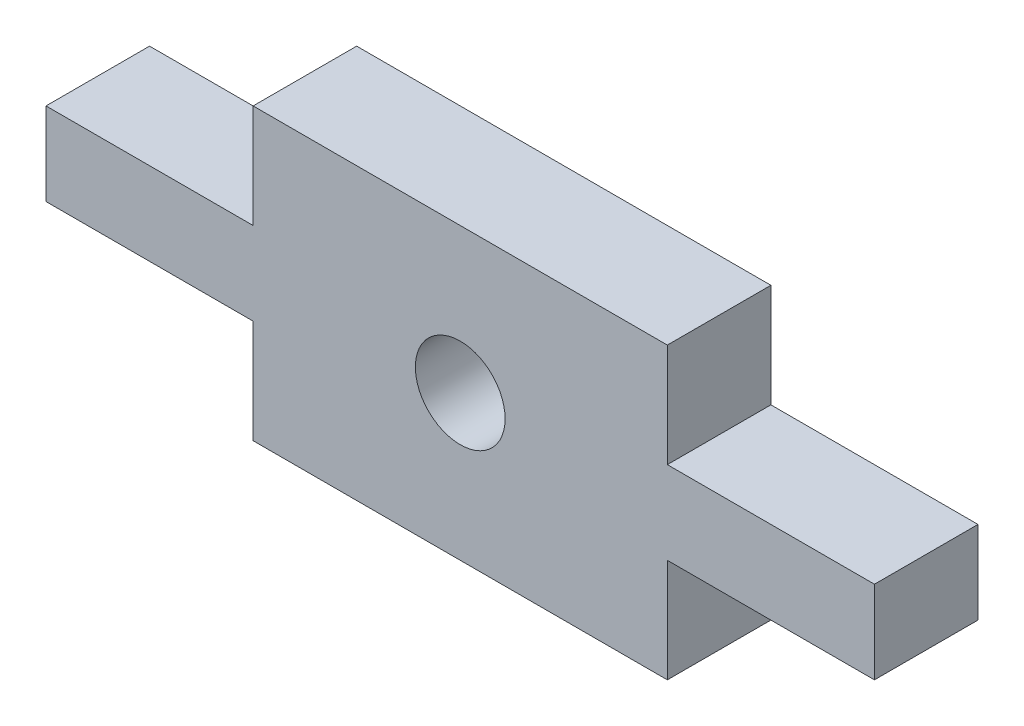
SolidWorks part; units mm, degrees
ref_plane "Front Plane" through (0, 0, 0) normal (0, 0, 1) x (1, 0, 0)
ref_plane "Top Plane" through (0, 0, 0) normal (0, 1, 0) x (1, 0, 0)
ref_plane "Right Plane" through (0, 0, 0) normal (1, 0, 0) x (0, 0, -1)
sketch "Model" plane through (0, 0, 0) normal (0, 0, 1) x (1, 0, 0)
  line L0 (50.0002, 37.8002) -> (62.0002, 37.8002)
  line L1 (50.0002, 43.2002) -> (44.0001, 43.2002)
  line L2 (50.0002, 46.2002) -> (50.0002, 43.2002)
  line L3 (62.0002, 46.2002) -> (50.0002, 46.2002)
  line L4 (62.0002, 43.2002) -> (62.0002, 46.2002)
  line L5 (68, 43.2002) -> (62.0002, 43.2002)
  line L6 (62.0002, 40.8002) -> (62.0002, 37.8002)
  line L7 (68, 40.8002) -> (62.0002, 40.8002)
  line L8 (50.0002, 40.8002) -> (50.0002, 37.8002)
  line L9 (44.0001, 40.8002) -> (50.0002, 40.8002)
  line L10 (68, 40.8002) -> (68, 43.2002)
  line L11 (44.0001, 43.2002) -> (44.0001, 40.8002)
  line L12 (44.0001, 42.0002) -> (68, 42.0002) construction
  circle A0 centre (56.0003, 42.0002) radius 1.3
  dimension "D1" = 12
  dimension "D2" = 3
  dimension "D3" = 2.4
  dimension "D4" = 3
extrude "Boss-Extrude1" add sketch "Model" along normal blind 3
